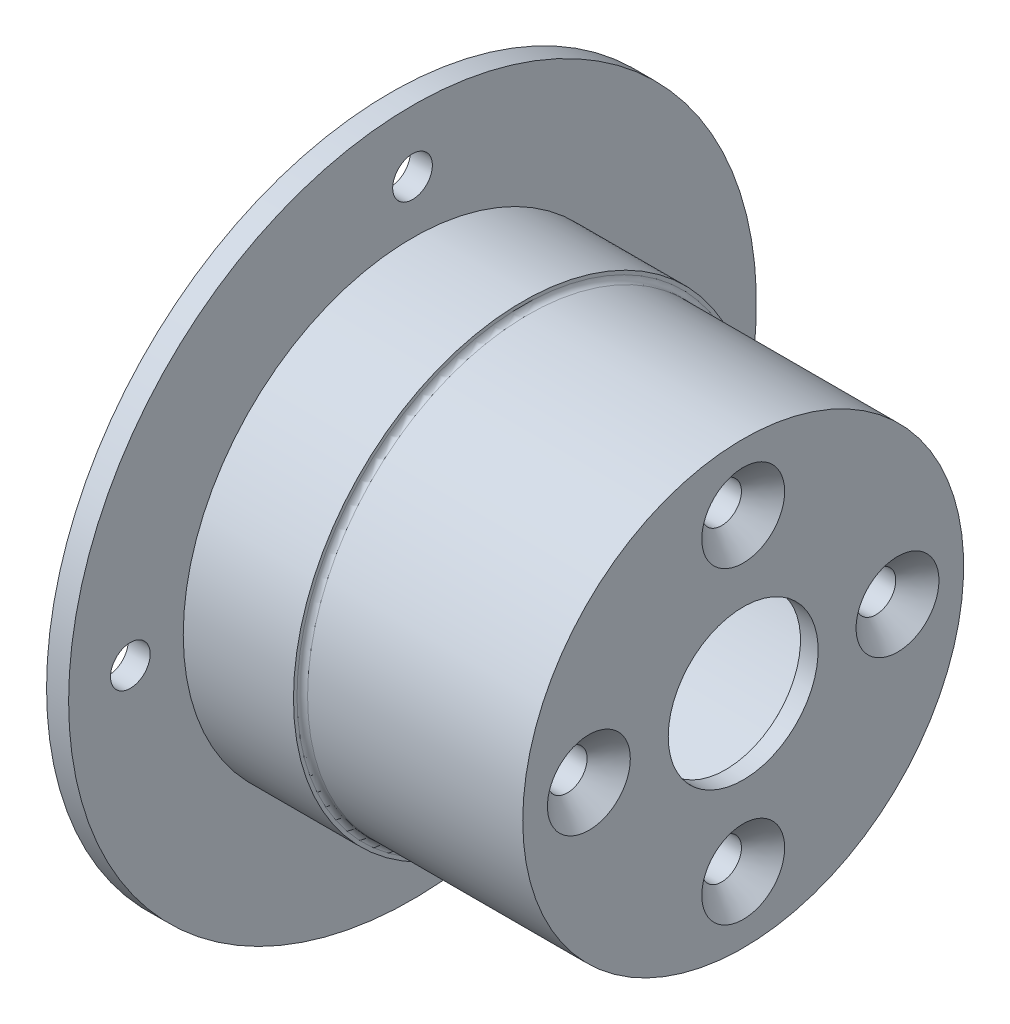
SolidWorks part; units mm, degrees
material "Nylon 6/10"
ref_plane "Front Plane" through (0, 0, 0) normal (0, 0, 1) x (1, 0, 0)
ref_plane "Top Plane" through (0, 0, 0) normal (0, 1, 0) x (1, 0, 0)
ref_plane "Right Plane" through (0, 0, 0) normal (1, 0, 0) x (0, 0, -1)
sketch "Sketch2" plane through (0, 0, 0) normal (0, 0, 1) x (1, 0, 0)
  line L0 (-64.1034, 0) -> (113.4236, 0) construction
  line L2 (0, 21) -> (35, 21)
  line L3 (0, -55) -> (0, 55) construction
  line L13 (35, 21) -> (35, 12.75)
  line L14 (35, 12.75) -> (38, 12.75)
  line L19 (15, 25) -> (15, 26)
  line L21 (0, 26) -> (0, 21)
  line L25 (40, 25) -> (15, 25)
  line L26 (15, 26) -> (2.5, 26)
  line L27 (2.5, 26) -> (2.5, 39)
  line L28 (2.5, 39) -> (0, 39)
  line L29 (0, 39) -> (0, 26)
  line L30 (38, 12.75) -> (38, 8.5)
  line L31 (38, 8.5) -> (40, 8.5)
  line L32 (40, 8.5) -> (40, 25)
  point P14 (36.5, 12.75)
  dimension "D1" = 21
  dimension "D2" = 35
  dimension "D3" = 12.75
  dimension "D4" = 3
  dimension "D5" = 25
  dimension "D6" = 26
  dimension "D7" = 2.5
  dimension "D8" = 39
  dimension "D9" = 15
  dimension "D10" = 8.5
  dimension "D11" = 2
revolve "Revolve1" add sketch "Sketch2" angle 360 about L0
hole_wizard "CSK for M4 Flat Head Machine Screw1" positions "Sketch7" profile "Sketch8" countersink size "M4" standard "ANSI Metric" end condition up to next
sketch "Sketch7" plane through (40, 0, 0) normal (1, 0, 0) x (0, 0, -1)
  circle A0 centre (0, 0) radius 17.5
  point P0 (0, 17.5)
  point P2 (17.5, 0)
  point P4 (0, -17.5)
  point P6 (-17.5, 0)
  dimension "D1" = 35
sketch "Sketch8" plane through (40, 17.5, 0) normal (0, 1, 0) x (0, 0, -1)
  line L0 (0, 0) -> (0, 5)
  line L1 (0, 5) -> (2.25, 5)
  line L2 (2.25, 5) -> (2.25, 2.45)
  line L3 (2.25, 2.45) -> (4.7, 0)
  line L5 (4.7, 0) -> (0, 0)
  line L6 (-2.25, 2.45) -> (-4.7, 0) construction
  line L11 (0, -6.35) -> (0, 107.95) construction
  dimension "Thru Hole Dia." = 4.5
  dimension "Thru Hole Depth" = 5
  dimension "Near C'Sink Dia." = 9.4
  dimension "Near C'Sink Angle" = 90
fillet "Fillet1" radius 0.6 1 edges at (15, 0, 25)
hole_wizard "M4 Clearance Hole1" positions "Sketch5" profile "Sketch6" hole size "M4" standard "ANSI Metric" end condition up to next
sketch "Sketch5" plane through (0, 0, 0) normal (-1, 0, 0) x (0, 0, 1)
  circle A0 centre (0, 0) radius 32
  point P0 (0, 32)
  point P2 (0, -32)
  point P4 (32, 0)
  point P6 (-32, 0)
  dimension "D1" = 64
sketch "Sketch6" plane through (0, 32, 0) normal (0, 1, 0) x (0, 0, 1)
  line L0 (0, 0) -> (0, 2.5)
  line L1 (0, 2.5) -> (2.25, 2.5)
  line L2 (2.25, 2.5) -> (2.25, 0)
  line L5 (2.25, 0) -> (0, 0)
  line L11 (0, -6.35) -> (0, 107.95) construction
  dimension "Thru Hole Dia." = 4.5
  dimension "Thru Hole Depth" = 2.5
